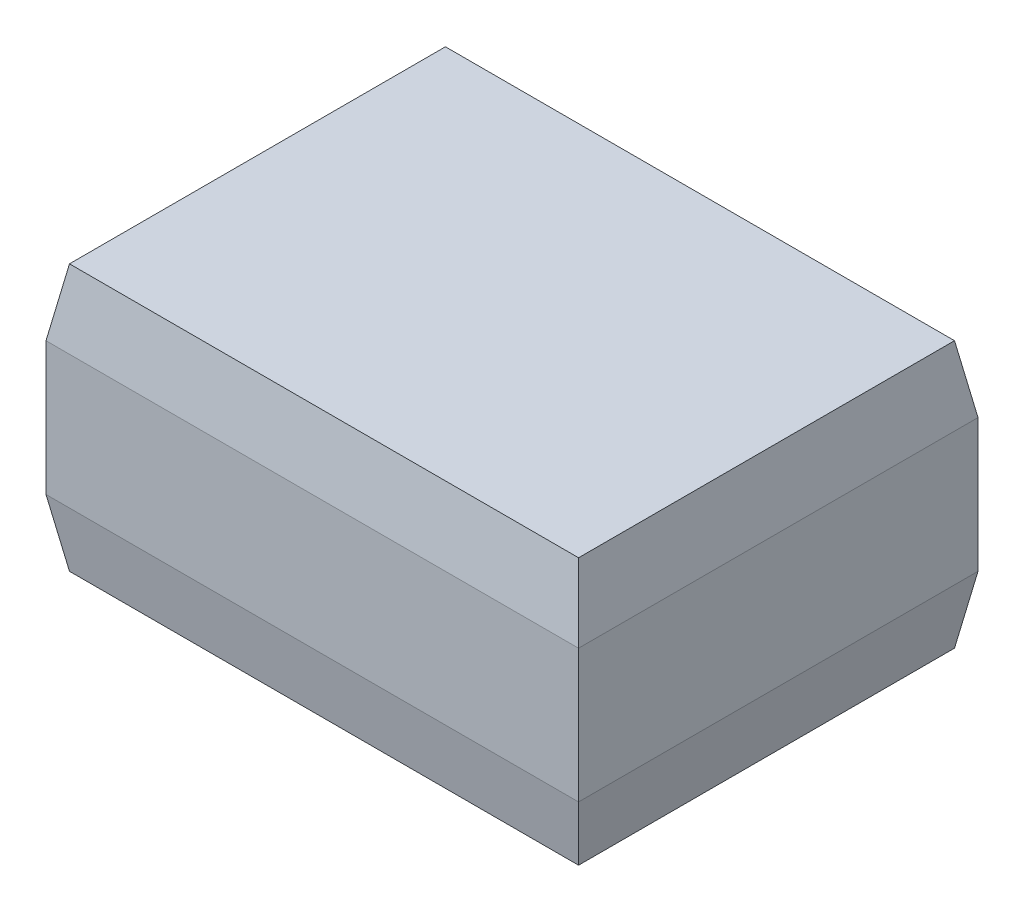
SolidWorks part; units mm, degrees
ref_plane "Plan de face" through (0, 0, 0) normal (0, 0, 1) x (1, 0, 0)
ref_plane "Plan de dessus" through (0, 0, 0) normal (0, 1, 0) x (1, 0, 0)
ref_plane "Plan de droite" through (0, 0, 0) normal (1, 0, 0) x (0, 0, -1)
sketch "Esquisse1" plane through (0, 0, 0) normal (0, 1, 0) x (1, 0, 0)
  line L1 (0, 0) -> (4, 0)
  line L2 (0, 0) -> (0, 3)
  line L3 (0, 3) -> (4, 3)
  line L4 (4, 0) -> (4, 3)
  dimension "D1" = 4
  dimension "D2" = 3
extrude "Extrusion1" add sketch "Esquisse1" along normal blind 2
chamfer "Chanfrein1" distance 0.5 angle 10 1 edges at (4, 2, -1.5)
chamfer "Chanfrein2" distance 0.5 angle 10 1 edges at (0, 2, -1.5)
chamfer "Chanfrein3" distance 0.5 angle 10 2 edges at (2, 2, -3) (2, 2, 0)
chamfer "Chanfrein4" distance 0.5 angle 10 1 edges at (4, 0, -1.5)
chamfer "Chanfrein5" distance 0.5 angle 10 3 edges at (1.9559, 0, -3) (0, 0, -1.5) (1.9559, 0, 0)
